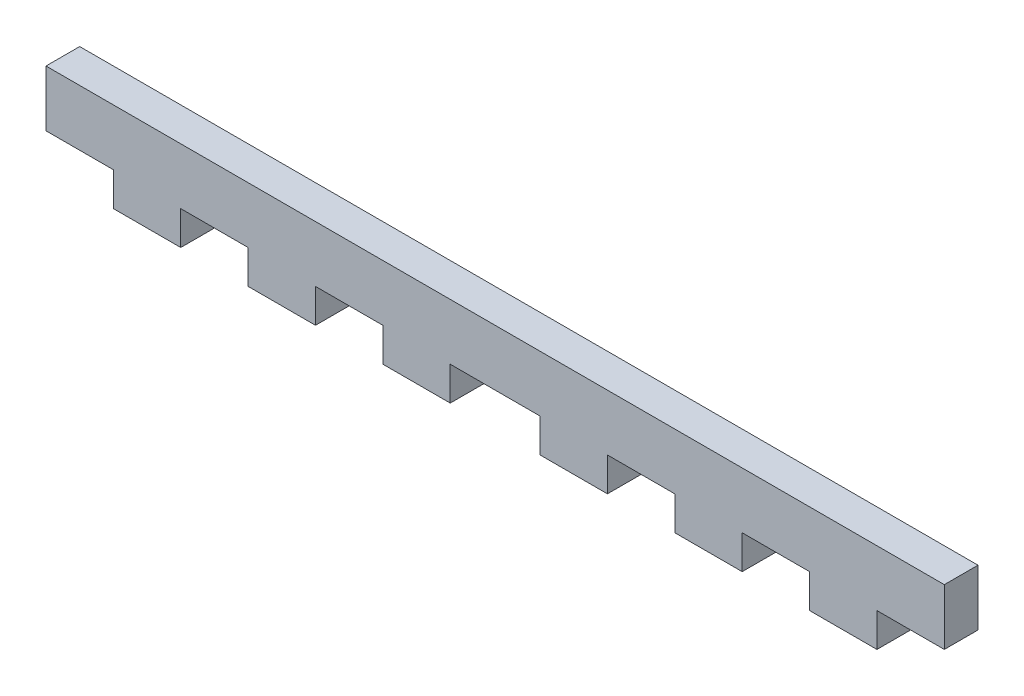
SolidWorks part; units mm, degrees
ref_plane "Front Plane" through (0, 0, 0) normal (0, 0, 1) x (1, 0, 0)
ref_plane "Top Plane" through (0, 0, 0) normal (0, 1, 0) x (1, 0, 0)
ref_plane "Right Plane" through (0, 0, 0) normal (1, 0, 0) x (0, 0, -1)
sketch "Sketch1" plane through (0, 0, 0) normal (0, 0, 1) x (1, 0, 0)
  line L0 (-49.149, 0) -> (47.9254, 0) construction
  line L1 (0, 43.1157) -> (0, -36.1345) construction
  line L3 (-33.3201, -10.7317) -> (46.6799, -10.7317)
  line L4 (-33.3201, -10.7317) -> (-33.3201, -5.7317)
  line L5 (-33.3201, -5.7317) -> (46.6799, -5.7317)
  line L6 (46.6799, -10.7317) -> (46.6799, -5.7317)
extrude "Boss-Extrude1" add sketch "Sketch1" along normal blind 3
sketch "Sketch2" plane through (0, 0, 3) normal (0, 0, 1) x (1, 0, 0)
  line L0 (-27.3201, -10.7317) -> (-21.3201, -10.7317)
  line L1 (40.6799, -10.7317) -> (40.6799, -13.7317)
  line L2 (40.6799, -13.7317) -> (34.6799, -13.7317)
  line L3 (34.6799, -13.7317) -> (34.6799, -10.7317)
  line L4 (-15.3201, -10.7317) -> (-9.3201, -10.7317)
  line L5 (28.6799, -10.7317) -> (28.6799, -13.7317)
  line L6 (28.6799, -13.7317) -> (22.6799, -13.7317)
  line L7 (22.6799, -13.7317) -> (22.6799, -10.7317)
  line L8 (-3.3201, -10.7317) -> (2.6799, -10.7317)
  line L9 (16.6799, -10.7317) -> (16.6799, -13.7317)
  line L10 (16.6799, -13.7317) -> (10.6799, -13.7317)
  line L11 (10.6799, -13.7317) -> (10.6799, -10.7317)
  line L12 (10.6799, -10.7317) -> (16.6799, -10.7317)
  line L13 (2.6799, -10.7317) -> (2.6799, -13.7317)
  line L14 (2.6799, -13.7317) -> (-3.3201, -13.7317)
  line L15 (-3.3201, -13.7317) -> (-3.3201, -10.7317)
  line L16 (22.6799, -10.7317) -> (28.6799, -10.7317)
  line L17 (-9.3201, -10.7317) -> (-9.3201, -13.7317)
  line L18 (-9.3201, -13.7317) -> (-15.3201, -13.7317)
  line L19 (-15.3201, -13.7317) -> (-15.3201, -10.7317)
  line L20 (34.6799, -10.7317) -> (40.6799, -10.7317)
  line L21 (-21.3201, -10.7317) -> (-21.3201, -13.7317)
  line L22 (-21.3201, -13.7317) -> (-27.3201, -13.7317)
  line L23 (-27.3201, -13.7317) -> (-27.3201, -10.7317)
extrude "Boss-Extrude2" add sketch "Sketch2" against normal blind 3
